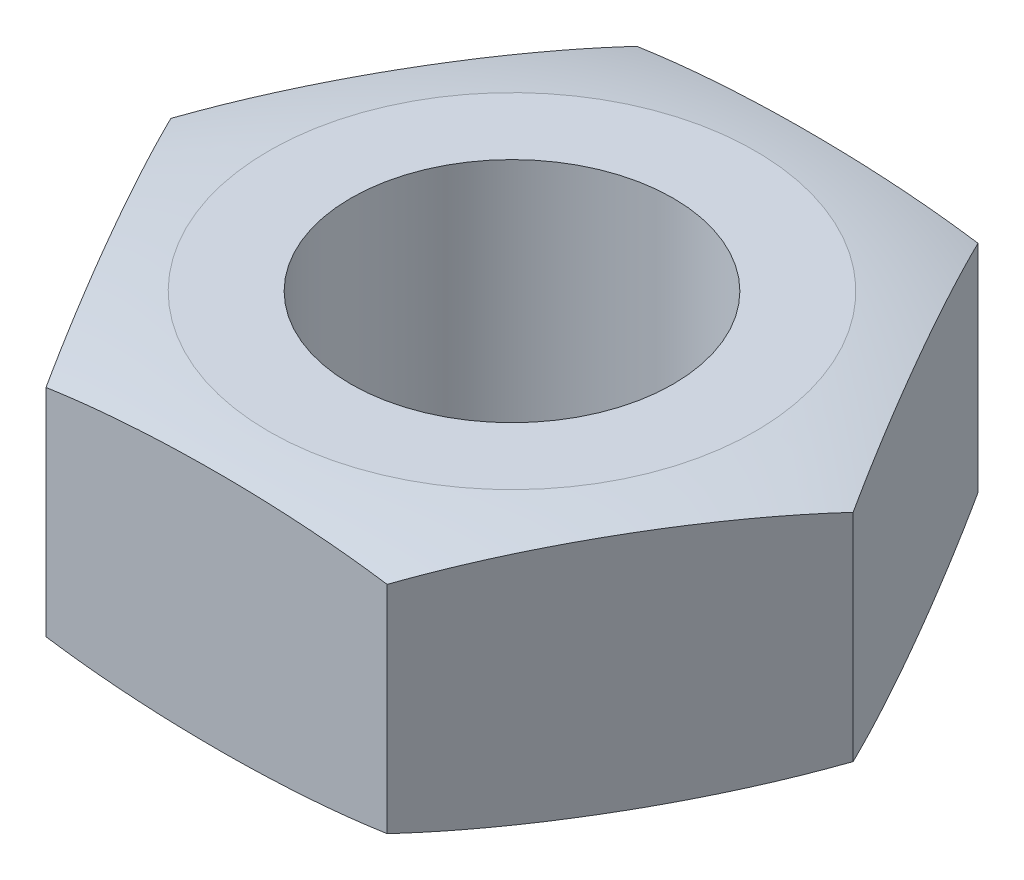
SolidWorks part; units mm, degrees
ref_plane "Plano frontal" through (0, 0, 0) normal (0, 0, 1) x (1, 0, 0)
ref_plane "Plano superior" through (0, 0, 0) normal (0, 1, 0) x (1, 0, 0)
ref_plane "Plano direito" through (0, 0, 0) normal (1, 0, 0) x (0, 0, -1)
sketch "Esboço1" plane through (0, 0, 0) normal (0, 1, 0) x (1, 0, 0)
  line L1 (3.1754, 0) -> (1.5877, 2.75)
  line L2 (1.5877, 2.75) -> (-1.5877, 2.75)
  line L3 (-1.5877, 2.75) -> (-3.1754, 0)
  line L4 (-3.1754, 0) -> (-1.5877, -2.75)
  line L5 (-1.5877, -2.75) -> (1.5877, -2.75)
  line L6 (1.5877, -2.75) -> (3.1754, 0)
  circle A0 centre (0, 0) radius 2.75 construction
  circle A1 centre (0, 0) radius 1.5
  dimension "D2" = 3
  dimension "D1" = 5.5
extrude "Ressalto-extrusão1" add sketch "Esboço1" along normal blind 2.4
sketch "Esboço3" plane through (0, 0, 0) normal (0, 0, 1) x (1, 0, 0)
  line L0 (1.5, 2.45) -> (1.5, 3.0395)
  line L1 (1.5, 3.0395) -> (3.5, 3.0395)
  line L2 (3.5, 3.0395) -> (3.5, 2.0973)
  line L3 (3.5, 0.3027) -> (3.5, -0.8371)
  line L4 (3.5, -0.8371) -> (1.5, -0.8371)
  line L5 (1.5, -0.8371) -> (1.5, -0.05)
  line L6 (1.5, 2.45) -> (-2.0985, 2.45)
  line L7 (3.5, 2.0973) -> (5.9023, 1.223)
  line L8 (3.5, 0.3027) -> (5.4683, 1.0191)
  line L9 (1.5, -0.05) -> (-1.0081, -0.05)
  line L10 (0, 0) -> (0, 8.4059) construction
  line L11 (-1.5877, 2.4) -> (1.5877, 2.4) construction
  line L12 (-1.5877, 0) -> (1.5877, 0) construction
  arc A0 (1.5, 2.45) -> (3.5, 2.0973) centre (1.5, -3.3976) cw
  arc A1 (1.5, -0.05) -> (3.5, 0.3027) centre (1.5, 5.7976) ccw
  dimension "D1" = 0.05
  dimension "D2" = 0.05
  dimension "D3" = 1.5
  dimension "D4" = 3.5
  dimension "D5" = 20
  dimension "D6" = 20
revolve "Corte-Revolução1" cut sketch "Esboço3" angle 360 about L10
